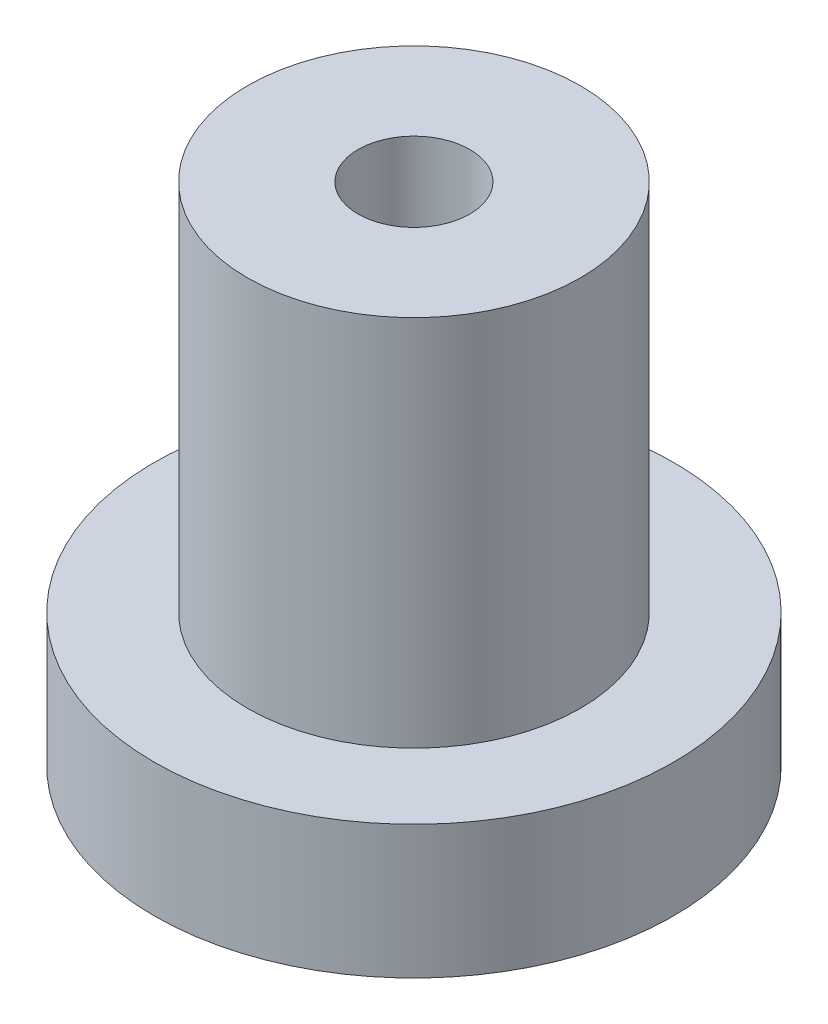
SolidWorks part; units mm, degrees
ref_plane "Alzado" through (0, 0, 0) normal (0, 0, 1) x (1, 0, 0)
ref_plane "Planta" through (0, 0, 0) normal (0, 1, 0) x (1, 0, 0)
ref_plane "Vista lateral" through (0, 0, 0) normal (1, 0, 0) x (0, 0, -1)
sketch "Croquis1" plane through (0, 0, 0) normal (0, 1, 0) x (1, 0, 0)
  circle A0 centre (0, 0) radius 9.75
  dimension "D1" = 19.5
extrude "Saliente-Extruir1" add sketch "Croquis1" along normal blind 5
sketch "Croquis2" plane through (0, 5, 0) normal (0, 1, 0) x (1, 0, 0)
  circle A0 centre (0, 0) radius 6.25
  dimension "D1" = 12.5
extrude "Saliente-Extruir2" add sketch "Croquis2" along normal blind 14
sketch "Croquis3" plane through (0, 19, 0) normal (0, 1, 0) x (1, 0, 0)
  circle A0 centre (0, 0) radius 2.1
  dimension "D1" = 4.2
extrude "Cortar-Extruir1" cut sketch "Croquis3" against normal blind 44
